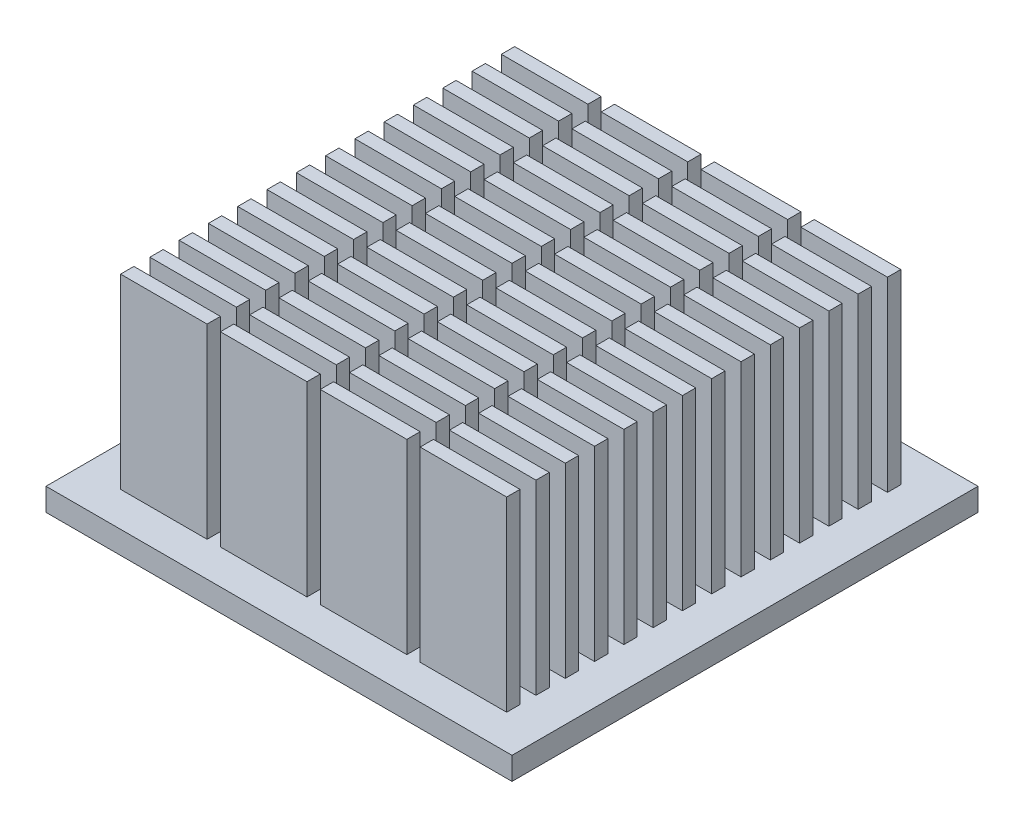
SolidWorks part; units mm, degrees
ref_plane "Front Plane" through (0, 0, 0) normal (0, 0, 1) x (1, 0, 0)
ref_plane "Top Plane" through (0, 0, 0) normal (0, 1, 0) x (1, 0, 0)
ref_plane "Right Plane" through (0, 0, 0) normal (1, 0, 0) x (0, 0, -1)
sketch "Sketch1" plane through (0, 0, 0) normal (0, 1, 0) x (1, 0, 0)
  line L1 (-17.5, -17.5) -> (17.5, -17.5)
  line L2 (-17.5, -17.5) -> (-17.5, 17.5)
  line L3 (-17.5, 17.5) -> (17.5, 17.5)
  line L4 (17.5, -17.5) -> (17.5, 17.5)
  line L5 (-17.5, -17.5) -> (17.5, 17.5) construction
  line L6 (-17.5, 17.5) -> (17.5, -17.5) construction
  point P0 (0, 0)
  dimension "D1" = 35
  dimension "D2" = 35
extrude "Boss-Extrude1" add sketch "Sketch1" along normal blind 1.7
sketch "Sketch2" plane through (0, 1.7, 0) normal (0, 1, 0) x (1, 0, 0)
  line L0 (-14.5, -0.7) -> (-8, -0.7)
  line L1 (-14.5, 1.5) -> (-8, 1.5)
  line L2 (-14.5, 1.5) -> (-14.5, 0.5)
  line L3 (-14.5, 0.5) -> (-8, 0.5)
  line L4 (-8, 1.5) -> (-8, 0.5)
  line L5 (-7, 1.5) -> (-0.5, 1.5)
  line L6 (-7, 1.5) -> (-7, 0.5)
  line L7 (-7, 0.5) -> (-0.5, 0.5)
  line L8 (-0.5, 1.5) -> (-0.5, 0.5)
  line L9 (0.5, 1.5) -> (7, 1.5)
  line L10 (0.5, 1.5) -> (0.5, 0.5)
  line L11 (0.5, 0.5) -> (7, 0.5)
  line L12 (7, 1.5) -> (7, 0.5)
  line L13 (8, 1.5) -> (14.5, 1.5)
  line L14 (8, 1.5) -> (8, 0.5)
  line L15 (8, 0.5) -> (14.5, 0.5)
  line L16 (14.5, 1.5) -> (14.5, 0.5)
  line L17 (-14.5, -0.7) -> (-14.5, -1.7)
  line L18 (-14.5, -1.7) -> (-8, -1.7)
  line L19 (-8, -0.7) -> (-8, -1.7)
  line L20 (-7, -0.7) -> (-0.5, -0.7)
  line L21 (-7, -0.7) -> (-7, -1.7)
  line L22 (-7, -1.7) -> (-0.5, -1.7)
  line L23 (-0.5, -0.7) -> (-0.5, -1.7)
  line L24 (0.5, -0.7) -> (7, -0.7)
  line L25 (0.5, -0.7) -> (0.5, -1.7)
  line L26 (0.5, -1.7) -> (7, -1.7)
  line L27 (7, -0.7) -> (7, -1.7)
  line L28 (8, -0.7) -> (14.5, -0.7)
  line L29 (8, -0.7) -> (8, -1.7)
  line L30 (8, -1.7) -> (14.5, -1.7)
  line L31 (14.5, -0.7) -> (14.5, -1.7)
  line L32 (-14.5, -2.9) -> (-8, -2.9)
  line L33 (-14.5, -2.9) -> (-14.5, -3.9)
  line L34 (-14.5, -3.9) -> (-8, -3.9)
  line L35 (-8, -2.9) -> (-8, -3.9)
  line L36 (-7, -2.9) -> (-0.5, -2.9)
  line L37 (-7, -2.9) -> (-7, -3.9)
  line L38 (-7, -3.9) -> (-0.5, -3.9)
  line L39 (-0.5, -2.9) -> (-0.5, -3.9)
  line L40 (0.5, -2.9) -> (7, -2.9)
  line L41 (0.5, -2.9) -> (0.5, -3.9)
  line L42 (0.5, -3.9) -> (7, -3.9)
  line L43 (7, -2.9) -> (7, -3.9)
  line L44 (8, -2.9) -> (14.5, -2.9)
  line L45 (8, -2.9) -> (8, -3.9)
  line L46 (8, -3.9) -> (14.5, -3.9)
  line L47 (14.5, -2.9) -> (14.5, -3.9)
  line L48 (-14.5, -5.1) -> (-8, -5.1)
  line L49 (-14.5, -5.1) -> (-14.5, -6.1)
  line L50 (-14.5, -6.1) -> (-8, -6.1)
  line L51 (-8, -5.1) -> (-8, -6.1)
  line L52 (-7, -5.1) -> (-0.5, -5.1)
  line L53 (-7, -5.1) -> (-7, -6.1)
  line L54 (-7, -6.1) -> (-0.5, -6.1)
  line L55 (-0.5, -5.1) -> (-0.5, -6.1)
  line L56 (0.5, -5.1) -> (7, -5.1)
  line L57 (0.5, -5.1) -> (0.5, -6.1)
  line L58 (0.5, -6.1) -> (7, -6.1)
  line L59 (7, -5.1) -> (7, -6.1)
  line L60 (8, -5.1) -> (14.5, -5.1)
  line L61 (8, -5.1) -> (8, -6.1)
  line L62 (8, -6.1) -> (14.5, -6.1)
  line L63 (14.5, -5.1) -> (14.5, -6.1)
  line L64 (-14.5, -7.3) -> (-8, -7.3)
  line L65 (-14.5, -7.3) -> (-14.5, -8.3)
  line L66 (-14.5, -8.3) -> (-8, -8.3)
  line L67 (-8, -7.3) -> (-8, -8.3)
  line L68 (-7, -7.3) -> (-0.5, -7.3)
  line L69 (-7, -7.3) -> (-7, -8.3)
  line L70 (-7, -8.3) -> (-0.5, -8.3)
  line L71 (-0.5, -7.3) -> (-0.5, -8.3)
  line L72 (0.5, -7.3) -> (7, -7.3)
  line L73 (0.5, -7.3) -> (0.5, -8.3)
  line L74 (0.5, -8.3) -> (7, -8.3)
  line L75 (7, -7.3) -> (7, -8.3)
  line L76 (8, -7.3) -> (14.5, -7.3)
  line L77 (8, -7.3) -> (8, -8.3)
  line L78 (8, -8.3) -> (14.5, -8.3)
  line L79 (14.5, -7.3) -> (14.5, -8.3)
  line L80 (-14.5, -9.5) -> (-8, -9.5)
  line L81 (-14.5, -9.5) -> (-14.5, -10.5)
  line L82 (-14.5, -10.5) -> (-8, -10.5)
  line L83 (-8, -9.5) -> (-8, -10.5)
  line L84 (-7, -9.5) -> (-0.5, -9.5)
  line L85 (-7, -9.5) -> (-7, -10.5)
  line L86 (-7, -10.5) -> (-0.5, -10.5)
  line L87 (-0.5, -9.5) -> (-0.5, -10.5)
  line L88 (0.5, -9.5) -> (7, -9.5)
  line L89 (0.5, -9.5) -> (0.5, -10.5)
  line L90 (0.5, -10.5) -> (7, -10.5)
  line L91 (7, -9.5) -> (7, -10.5)
  line L92 (8, -9.5) -> (14.5, -9.5)
  line L93 (8, -9.5) -> (8, -10.5)
  line L94 (8, -10.5) -> (14.5, -10.5)
  line L95 (14.5, -9.5) -> (14.5, -10.5)
  line L96 (-14.5, -11.7) -> (-8, -11.7)
  line L97 (-14.5, -11.7) -> (-14.5, -12.7)
  line L98 (-14.5, -12.7) -> (-8, -12.7)
  line L99 (-8, -11.7) -> (-8, -12.7)
  line L100 (-7, -11.7) -> (-0.5, -11.7)
  line L101 (-7, -11.7) -> (-7, -12.7)
  line L102 (-7, -12.7) -> (-0.5, -12.7)
  line L103 (-0.5, -11.7) -> (-0.5, -12.7)
  line L104 (0.5, -11.7) -> (7, -11.7)
  line L105 (0.5, -11.7) -> (0.5, -12.7)
  line L106 (0.5, -12.7) -> (7, -12.7)
  line L107 (7, -11.7) -> (7, -12.7)
  line L108 (8, -11.7) -> (14.5, -11.7)
  line L109 (8, -11.7) -> (8, -12.7)
  line L110 (8, -12.7) -> (14.5, -12.7)
  line L111 (14.5, -11.7) -> (14.5, -12.7)
  line L112 (-14.5, -13.9) -> (-8, -13.9)
  line L113 (-14.5, -13.9) -> (-14.5, -14.9)
  line L114 (-14.5, -14.9) -> (-8, -14.9)
  line L115 (-8, -13.9) -> (-8, -14.9)
  line L116 (-7, -13.9) -> (-0.5, -13.9)
  line L117 (-7, -13.9) -> (-7, -14.9)
  line L118 (-7, -14.9) -> (-0.5, -14.9)
  line L119 (-0.5, -13.9) -> (-0.5, -14.9)
  line L120 (0.5, -13.9) -> (7, -13.9)
  line L121 (0.5, -13.9) -> (0.5, -14.9)
  line L122 (0.5, -14.9) -> (7, -14.9)
  line L123 (7, -13.9) -> (7, -14.9)
  line L124 (8, -13.9) -> (14.5, -13.9)
  line L125 (8, -13.9) -> (8, -14.9)
  line L126 (8, -14.9) -> (14.5, -14.9)
  line L127 (14.5, -13.9) -> (14.5, -14.9)
  line L128 (-14.5, 1.5) -> (-8, 1.5)
  line L129 (-14.5, 1.5) -> (-14.5, 0.5)
  line L130 (-14.5, 0.5) -> (-8, 0.5)
  line L131 (-8, 1.5) -> (-8, 0.5)
  line L132 (-7, 1.5) -> (-0.5, 1.5)
  line L133 (-7, 1.5) -> (-7, 0.5)
  line L134 (-7, 0.5) -> (-0.5, 0.5)
  line L135 (-0.5, 1.5) -> (-0.5, 0.5)
  line L136 (0.5, 1.5) -> (7, 1.5)
  line L137 (0.5, 1.5) -> (0.5, 0.5)
  line L138 (0.5, 0.5) -> (7, 0.5)
  line L139 (7, 1.5) -> (7, 0.5)
  line L140 (8, 1.5) -> (14.5, 1.5)
  line L141 (8, 1.5) -> (8, 0.5)
  line L142 (8, 0.5) -> (14.5, 0.5)
  line L143 (14.5, 1.5) -> (14.5, 0.5)
  line L144 (-14.5, -0.7) -> (-8, -0.7)
  line L145 (-14.5, -0.7) -> (-14.5, -1.7)
  line L146 (-14.5, -1.7) -> (-8, -1.7)
  line L147 (-8, -0.7) -> (-8, -1.7)
  line L148 (-7, -0.7) -> (-0.5, -0.7)
  line L149 (-7, -0.7) -> (-7, -1.7)
  line L150 (-7, -1.7) -> (-0.5, -1.7)
  line L151 (-0.5, -0.7) -> (-0.5, -1.7)
  line L152 (0.5, -0.7) -> (7, -0.7)
  line L153 (0.5, -0.7) -> (0.5, -1.7)
  line L154 (0.5, -1.7) -> (7, -1.7)
  line L155 (7, -0.7) -> (7, -1.7)
  line L156 (8, -0.7) -> (14.5, -0.7)
  line L157 (8, -0.7) -> (8, -1.7)
  line L158 (8, -1.7) -> (14.5, -1.7)
  line L159 (14.5, -0.7) -> (14.5, -1.7)
  line L160 (-14.5, -2.9) -> (-8, -2.9)
  line L161 (-14.5, -2.9) -> (-14.5, -3.9)
  line L162 (-14.5, -3.9) -> (-8, -3.9)
  line L163 (-8, -2.9) -> (-8, -3.9)
  line L164 (-7, -2.9) -> (-0.5, -2.9)
  line L165 (-7, -2.9) -> (-7, -3.9)
  line L166 (-7, -3.9) -> (-0.5, -3.9)
  line L167 (-0.5, -2.9) -> (-0.5, -3.9)
  line L168 (0.5, -2.9) -> (7, -2.9)
  line L169 (0.5, -2.9) -> (0.5, -3.9)
  line L170 (0.5, -3.9) -> (7, -3.9)
  line L171 (7, -2.9) -> (7, -3.9)
  line L172 (8, -2.9) -> (14.5, -2.9)
  line L173 (8, -2.9) -> (8, -3.9)
  line L174 (8, -3.9) -> (14.5, -3.9)
  line L175 (14.5, -2.9) -> (14.5, -3.9)
  line L176 (-14.5, -5.1) -> (-8, -5.1)
  line L177 (-14.5, -5.1) -> (-14.5, -6.1)
  line L178 (-14.5, -6.1) -> (-8, -6.1)
  line L179 (-8, -5.1) -> (-8, -6.1)
  line L180 (-7, -5.1) -> (-0.5, -5.1)
  line L181 (-7, -5.1) -> (-7, -6.1)
  line L182 (-7, -6.1) -> (-0.5, -6.1)
  line L183 (-0.5, -5.1) -> (-0.5, -6.1)
  line L184 (0.5, -5.1) -> (7, -5.1)
  line L185 (0.5, -5.1) -> (0.5, -6.1)
  line L186 (0.5, -6.1) -> (7, -6.1)
  line L187 (7, -5.1) -> (7, -6.1)
  line L188 (8, -5.1) -> (14.5, -5.1)
  line L189 (8, -5.1) -> (8, -6.1)
  line L190 (8, -6.1) -> (14.5, -6.1)
  line L191 (14.5, -5.1) -> (14.5, -6.1)
  line L192 (-14.5, -7.3) -> (-8, -7.3)
  line L193 (-14.5, -7.3) -> (-14.5, -8.3)
  line L194 (-14.5, -8.3) -> (-8, -8.3)
  line L195 (-8, -7.3) -> (-8, -8.3)
  line L196 (-7, -7.3) -> (-0.5, -7.3)
  line L197 (-7, -7.3) -> (-7, -8.3)
  line L198 (-7, -8.3) -> (-0.5, -8.3)
  line L199 (-0.5, -7.3) -> (-0.5, -8.3)
  line L200 (0.5, -7.3) -> (7, -7.3)
  line L201 (0.5, -7.3) -> (0.5, -8.3)
  line L202 (0.5, -8.3) -> (7, -8.3)
  line L203 (7, -7.3) -> (7, -8.3)
  line L204 (8, -7.3) -> (14.5, -7.3)
  line L205 (8, -7.3) -> (8, -8.3)
  line L206 (8, -8.3) -> (14.5, -8.3)
  line L207 (14.5, -7.3) -> (14.5, -8.3)
  line L208 (-14.5, -9.5) -> (-8, -9.5)
  line L209 (-14.5, -9.5) -> (-14.5, -10.5)
  line L210 (-14.5, -10.5) -> (-8, -10.5)
  line L211 (-8, -9.5) -> (-8, -10.5)
  line L212 (-7, -9.5) -> (-0.5, -9.5)
  line L213 (-7, -9.5) -> (-7, -10.5)
  line L214 (-7, -10.5) -> (-0.5, -10.5)
  line L215 (-0.5, -9.5) -> (-0.5, -10.5)
  line L216 (0.5, -9.5) -> (7, -9.5)
  line L217 (0.5, -9.5) -> (0.5, -10.5)
  line L218 (0.5, -10.5) -> (7, -10.5)
  line L219 (7, -9.5) -> (7, -10.5)
  line L220 (8, -9.5) -> (14.5, -9.5)
  line L221 (8, -9.5) -> (8, -10.5)
  line L222 (8, -10.5) -> (14.5, -10.5)
  line L223 (14.5, -9.5) -> (14.5, -10.5)
  line L224 (-14.5, -11.7) -> (-8, -11.7)
  line L225 (-14.5, -11.7) -> (-14.5, -12.7)
  line L226 (-14.5, -12.7) -> (-8, -12.7)
  line L227 (-8, -11.7) -> (-8, -12.7)
  line L228 (-7, -11.7) -> (-0.5, -11.7)
  line L229 (-7, -11.7) -> (-7, -12.7)
  line L230 (-7, -12.7) -> (-0.5, -12.7)
  line L231 (-0.5, -11.7) -> (-0.5, -12.7)
  line L232 (0.5, -11.7) -> (7, -11.7)
  line L233 (0.5, -11.7) -> (0.5, -12.7)
  line L234 (0.5, -12.7) -> (7, -12.7)
  line L235 (7, -11.7) -> (7, -12.7)
  line L236 (8, -11.7) -> (14.5, -11.7)
  line L237 (8, -11.7) -> (8, -12.7)
  line L238 (8, -12.7) -> (14.5, -12.7)
  line L239 (14.5, -11.7) -> (14.5, -12.7)
  line L240 (-14.5, 3.7) -> (-8, 3.7)
  line L241 (-14.5, 3.7) -> (-14.5, 2.7)
  line L242 (-14.5, 2.7) -> (-8, 2.7)
  line L243 (-8, 3.7) -> (-8, 2.7)
  line L244 (-7, 3.7) -> (-0.5, 3.7)
  line L245 (-7, 3.7) -> (-7, 2.7)
  line L246 (-7, 2.7) -> (-0.5, 2.7)
  line L247 (-0.5, 3.7) -> (-0.5, 2.7)
  line L248 (0.5, 3.7) -> (7, 3.7)
  line L249 (0.5, 3.7) -> (0.5, 2.7)
  line L250 (0.5, 2.7) -> (7, 2.7)
  line L251 (7, 3.7) -> (7, 2.7)
  line L252 (8, 3.7) -> (14.5, 3.7)
  line L253 (8, 3.7) -> (8, 2.7)
  line L254 (8, 2.7) -> (14.5, 2.7)
  line L255 (14.5, 3.7) -> (14.5, 2.7)
  line L256 (-14.5, 1.5) -> (-8, 1.5)
  line L257 (-14.5, 1.5) -> (-14.5, 0.5)
  line L258 (-14.5, 0.5) -> (-8, 0.5)
  line L259 (-8, 1.5) -> (-8, 0.5)
  line L260 (-7, 1.5) -> (-0.5, 1.5)
  line L261 (-7, 1.5) -> (-7, 0.5)
  line L262 (-7, 0.5) -> (-0.5, 0.5)
  line L263 (-0.5, 1.5) -> (-0.5, 0.5)
  line L264 (0.5, 1.5) -> (7, 1.5)
  line L265 (0.5, 1.5) -> (0.5, 0.5)
  line L266 (0.5, 0.5) -> (7, 0.5)
  line L267 (7, 1.5) -> (7, 0.5)
  line L268 (8, 1.5) -> (14.5, 1.5)
  line L269 (8, 1.5) -> (8, 0.5)
  line L270 (8, 0.5) -> (14.5, 0.5)
  line L271 (14.5, 1.5) -> (14.5, 0.5)
  line L272 (-14.5, -0.7) -> (-8, -0.7)
  line L273 (-14.5, -0.7) -> (-14.5, -1.7)
  line L274 (-14.5, -1.7) -> (-8, -1.7)
  line L275 (-8, -0.7) -> (-8, -1.7)
  line L276 (-7, -0.7) -> (-0.5, -0.7)
  line L277 (-7, -0.7) -> (-7, -1.7)
  line L278 (-7, -1.7) -> (-0.5, -1.7)
  line L279 (-0.5, -0.7) -> (-0.5, -1.7)
  line L280 (0.5, -0.7) -> (7, -0.7)
  line L281 (0.5, -0.7) -> (0.5, -1.7)
  line L282 (0.5, -1.7) -> (7, -1.7)
  line L283 (7, -0.7) -> (7, -1.7)
  line L284 (8, -0.7) -> (14.5, -0.7)
  line L285 (8, -0.7) -> (8, -1.7)
  line L286 (8, -1.7) -> (14.5, -1.7)
  line L287 (14.5, -0.7) -> (14.5, -1.7)
  line L288 (-14.5, -2.9) -> (-8, -2.9)
  line L289 (-14.5, -2.9) -> (-14.5, -3.9)
  line L290 (-14.5, -3.9) -> (-8, -3.9)
  line L291 (-8, -2.9) -> (-8, -3.9)
  line L292 (-7, -2.9) -> (-0.5, -2.9)
  line L293 (-7, -2.9) -> (-7, -3.9)
  line L294 (-7, -3.9) -> (-0.5, -3.9)
  line L295 (-0.5, -2.9) -> (-0.5, -3.9)
  line L296 (0.5, -2.9) -> (7, -2.9)
  line L297 (0.5, -2.9) -> (0.5, -3.9)
  line L298 (0.5, -3.9) -> (7, -3.9)
  line L299 (7, -2.9) -> (7, -3.9)
  line L300 (8, -2.9) -> (14.5, -2.9)
  line L301 (8, -2.9) -> (8, -3.9)
  line L302 (8, -3.9) -> (14.5, -3.9)
  line L303 (14.5, -2.9) -> (14.5, -3.9)
  line L304 (-14.5, -5.1) -> (-8, -5.1)
  line L305 (-14.5, -5.1) -> (-14.5, -6.1)
  line L306 (-14.5, -6.1) -> (-8, -6.1)
  line L307 (-8, -5.1) -> (-8, -6.1)
  line L308 (-7, -5.1) -> (-0.5, -5.1)
  line L309 (-7, -5.1) -> (-7, -6.1)
  line L310 (-7, -6.1) -> (-0.5, -6.1)
  line L311 (-0.5, -5.1) -> (-0.5, -6.1)
  line L312 (0.5, -5.1) -> (7, -5.1)
  line L313 (0.5, -5.1) -> (0.5, -6.1)
  line L314 (0.5, -6.1) -> (7, -6.1)
  line L315 (7, -5.1) -> (7, -6.1)
  line L316 (8, -5.1) -> (14.5, -5.1)
  line L317 (8, -5.1) -> (8, -6.1)
  line L318 (8, -6.1) -> (14.5, -6.1)
  line L319 (14.5, -5.1) -> (14.5, -6.1)
  line L320 (-14.5, -7.3) -> (-8, -7.3)
  line L321 (-14.5, -7.3) -> (-14.5, -8.3)
  line L322 (-14.5, -8.3) -> (-8, -8.3)
  line L323 (-8, -7.3) -> (-8, -8.3)
  line L324 (-7, -7.3) -> (-0.5, -7.3)
  line L325 (-7, -7.3) -> (-7, -8.3)
  line L326 (-7, -8.3) -> (-0.5, -8.3)
  line L327 (-0.5, -7.3) -> (-0.5, -8.3)
  line L328 (0.5, -7.3) -> (7, -7.3)
  line L329 (0.5, -7.3) -> (0.5, -8.3)
  line L330 (0.5, -8.3) -> (7, -8.3)
  line L331 (7, -7.3) -> (7, -8.3)
  line L332 (8, -7.3) -> (14.5, -7.3)
  line L333 (8, -7.3) -> (8, -8.3)
  line L334 (8, -8.3) -> (14.5, -8.3)
  line L335 (14.5, -7.3) -> (14.5, -8.3)
  line L336 (-14.5, -9.5) -> (-8, -9.5)
  line L337 (-14.5, -9.5) -> (-14.5, -10.5)
  line L338 (-14.5, -10.5) -> (-8, -10.5)
  line L339 (-8, -9.5) -> (-8, -10.5)
  line L340 (-7, -9.5) -> (-0.5, -9.5)
  line L341 (-7, -9.5) -> (-7, -10.5)
  line L342 (-7, -10.5) -> (-0.5, -10.5)
  line L343 (-0.5, -9.5) -> (-0.5, -10.5)
  line L344 (0.5, -9.5) -> (7, -9.5)
  line L345 (0.5, -9.5) -> (0.5, -10.5)
  line L346 (0.5, -10.5) -> (7, -10.5)
  line L347 (7, -9.5) -> (7, -10.5)
  line L348 (8, -9.5) -> (14.5, -9.5)
  line L349 (8, -9.5) -> (8, -10.5)
  line L350 (8, -10.5) -> (14.5, -10.5)
  line L351 (14.5, -9.5) -> (14.5, -10.5)
  line L352 (-14.5, 5.9) -> (-8, 5.9)
  line L353 (-14.5, 5.9) -> (-14.5, 4.9)
  line L354 (-14.5, 4.9) -> (-8, 4.9)
  line L355 (-8, 5.9) -> (-8, 4.9)
  line L356 (-7, 5.9) -> (-0.5, 5.9)
  line L357 (-7, 5.9) -> (-7, 4.9)
  line L358 (-7, 4.9) -> (-0.5, 4.9)
  line L359 (-0.5, 5.9) -> (-0.5, 4.9)
  line L360 (0.5, 5.9) -> (7, 5.9)
  line L361 (0.5, 5.9) -> (0.5, 4.9)
  line L362 (0.5, 4.9) -> (7, 4.9)
  line L363 (7, 5.9) -> (7, 4.9)
  line L364 (8, 5.9) -> (14.5, 5.9)
  line L365 (8, 5.9) -> (8, 4.9)
  line L366 (8, 4.9) -> (14.5, 4.9)
  line L367 (14.5, 5.9) -> (14.5, 4.9)
  line L368 (-14.5, 3.7) -> (-8, 3.7)
  line L369 (-14.5, 3.7) -> (-14.5, 2.7)
  line L370 (-14.5, 2.7) -> (-8, 2.7)
  line L371 (-8, 3.7) -> (-8, 2.7)
  line L372 (-7, 3.7) -> (-0.5, 3.7)
  line L373 (-7, 3.7) -> (-7, 2.7)
  line L374 (-7, 2.7) -> (-0.5, 2.7)
  line L375 (-0.5, 3.7) -> (-0.5, 2.7)
  line L376 (0.5, 3.7) -> (7, 3.7)
  line L377 (0.5, 3.7) -> (0.5, 2.7)
  line L378 (0.5, 2.7) -> (7, 2.7)
  line L379 (7, 3.7) -> (7, 2.7)
  line L380 (8, 3.7) -> (14.5, 3.7)
  line L381 (8, 3.7) -> (8, 2.7)
  line L382 (8, 2.7) -> (14.5, 2.7)
  line L383 (14.5, 3.7) -> (14.5, 2.7)
  line L384 (-14.5, 1.5) -> (-8, 1.5)
  line L385 (-14.5, 1.5) -> (-14.5, 0.5)
  line L386 (-14.5, 0.5) -> (-8, 0.5)
  line L387 (-8, 1.5) -> (-8, 0.5)
  line L388 (-7, 1.5) -> (-0.5, 1.5)
  line L389 (-7, 1.5) -> (-7, 0.5)
  line L390 (-7, 0.5) -> (-0.5, 0.5)
  line L391 (-0.5, 1.5) -> (-0.5, 0.5)
  line L392 (0.5, 1.5) -> (7, 1.5)
  line L393 (0.5, 1.5) -> (0.5, 0.5)
  line L394 (0.5, 0.5) -> (7, 0.5)
  line L395 (7, 1.5) -> (7, 0.5)
  line L396 (8, 1.5) -> (14.5, 1.5)
  line L397 (8, 1.5) -> (8, 0.5)
  line L398 (8, 0.5) -> (14.5, 0.5)
  line L399 (14.5, 1.5) -> (14.5, 0.5)
  line L400 (-14.5, -0.7) -> (-8, -0.7)
  line L401 (-14.5, -0.7) -> (-14.5, -1.7)
  line L402 (-14.5, -1.7) -> (-8, -1.7)
  line L403 (-8, -0.7) -> (-8, -1.7)
  line L404 (-7, -0.7) -> (-0.5, -0.7)
  line L405 (-7, -0.7) -> (-7, -1.7)
  line L406 (-7, -1.7) -> (-0.5, -1.7)
  line L407 (-0.5, -0.7) -> (-0.5, -1.7)
  line L408 (0.5, -0.7) -> (7, -0.7)
  line L409 (0.5, -0.7) -> (0.5, -1.7)
  line L410 (0.5, -1.7) -> (7, -1.7)
  line L411 (7, -0.7) -> (7, -1.7)
  line L412 (8, -0.7) -> (14.5, -0.7)
  line L413 (8, -0.7) -> (8, -1.7)
  line L414 (8, -1.7) -> (14.5, -1.7)
  line L415 (14.5, -0.7) -> (14.5, -1.7)
  line L416 (-14.5, -2.9) -> (-8, -2.9)
  line L417 (-14.5, -2.9) -> (-14.5, -3.9)
  line L418 (-14.5, -3.9) -> (-8, -3.9)
  line L419 (-8, -2.9) -> (-8, -3.9)
  line L420 (-7, -2.9) -> (-0.5, -2.9)
  line L421 (-7, -2.9) -> (-7, -3.9)
  line L422 (-7, -3.9) -> (-0.5, -3.9)
  line L423 (-0.5, -2.9) -> (-0.5, -3.9)
  line L424 (0.5, -2.9) -> (7, -2.9)
  line L425 (0.5, -2.9) -> (0.5, -3.9)
  line L426 (0.5, -3.9) -> (7, -3.9)
  line L427 (7, -2.9) -> (7, -3.9)
  line L428 (8, -2.9) -> (14.5, -2.9)
  line L429 (8, -2.9) -> (8, -3.9)
  line L430 (8, -3.9) -> (14.5, -3.9)
  line L431 (14.5, -2.9) -> (14.5, -3.9)
  line L432 (-14.5, -5.1) -> (-8, -5.1)
  line L433 (-14.5, -5.1) -> (-14.5, -6.1)
  line L434 (-14.5, -6.1) -> (-8, -6.1)
  line L435 (-8, -5.1) -> (-8, -6.1)
  line L436 (-7, -5.1) -> (-0.5, -5.1)
  line L437 (-7, -5.1) -> (-7, -6.1)
  line L438 (-7, -6.1) -> (-0.5, -6.1)
  line L439 (-0.5, -5.1) -> (-0.5, -6.1)
  line L440 (0.5, -5.1) -> (7, -5.1)
  line L441 (0.5, -5.1) -> (0.5, -6.1)
  line L442 (0.5, -6.1) -> (7, -6.1)
  line L443 (7, -5.1) -> (7, -6.1)
  line L444 (8, -5.1) -> (14.5, -5.1)
  line L445 (8, -5.1) -> (8, -6.1)
  line L446 (8, -6.1) -> (14.5, -6.1)
  line L447 (14.5, -5.1) -> (14.5, -6.1)
  line L448 (-14.5, -7.3) -> (-8, -7.3)
  line L449 (-14.5, -7.3) -> (-14.5, -8.3)
  line L450 (-14.5, -8.3) -> (-8, -8.3)
  line L451 (-8, -7.3) -> (-8, -8.3)
  line L452 (-7, -7.3) -> (-0.5, -7.3)
  line L453 (-7, -7.3) -> (-7, -8.3)
  line L454 (-7, -8.3) -> (-0.5, -8.3)
  line L455 (-0.5, -7.3) -> (-0.5, -8.3)
  line L456 (0.5, -7.3) -> (7, -7.3)
  line L457 (0.5, -7.3) -> (0.5, -8.3)
  line L458 (0.5, -8.3) -> (7, -8.3)
  line L459 (7, -7.3) -> (7, -8.3)
  line L460 (8, -7.3) -> (14.5, -7.3)
  line L461 (8, -7.3) -> (8, -8.3)
  line L462 (8, -8.3) -> (14.5, -8.3)
  line L463 (14.5, -7.3) -> (14.5, -8.3)
  line L464 (-14.5, 8.1) -> (-8, 8.1)
  line L465 (-14.5, 8.1) -> (-14.5, 7.1)
  line L466 (-14.5, 7.1) -> (-8, 7.1)
  line L467 (-8, 8.1) -> (-8, 7.1)
  line L468 (-7, 8.1) -> (-0.5, 8.1)
  line L469 (-7, 8.1) -> (-7, 7.1)
  line L470 (-7, 7.1) -> (-0.5, 7.1)
  line L471 (-0.5, 8.1) -> (-0.5, 7.1)
  line L472 (0.5, 8.1) -> (7, 8.1)
  line L473 (0.5, 8.1) -> (0.5, 7.1)
  line L474 (0.5, 7.1) -> (7, 7.1)
  line L475 (7, 8.1) -> (7, 7.1)
  line L476 (8, 8.1) -> (14.5, 8.1)
  line L477 (8, 8.1) -> (8, 7.1)
  line L478 (8, 7.1) -> (14.5, 7.1)
  line L479 (14.5, 8.1) -> (14.5, 7.1)
  line L480 (-14.5, 5.9) -> (-8, 5.9)
  line L481 (-14.5, 5.9) -> (-14.5, 4.9)
  line L482 (-14.5, 4.9) -> (-8, 4.9)
  line L483 (-8, 5.9) -> (-8, 4.9)
  line L484 (-7, 5.9) -> (-0.5, 5.9)
  line L485 (-7, 5.9) -> (-7, 4.9)
  line L486 (-7, 4.9) -> (-0.5, 4.9)
  line L487 (-0.5, 5.9) -> (-0.5, 4.9)
  line L488 (0.5, 5.9) -> (7, 5.9)
  line L489 (0.5, 5.9) -> (0.5, 4.9)
  line L490 (0.5, 4.9) -> (7, 4.9)
  line L491 (7, 5.9) -> (7, 4.9)
  line L492 (8, 5.9) -> (14.5, 5.9)
  line L493 (8, 5.9) -> (8, 4.9)
  line L494 (8, 4.9) -> (14.5, 4.9)
  line L495 (14.5, 5.9) -> (14.5, 4.9)
  line L496 (-14.5, 3.7) -> (-8, 3.7)
  line L497 (-14.5, 3.7) -> (-14.5, 2.7)
  line L498 (-14.5, 2.7) -> (-8, 2.7)
  line L499 (-8, 3.7) -> (-8, 2.7)
  line L500 (-7, 3.7) -> (-0.5, 3.7)
  line L501 (-7, 3.7) -> (-7, 2.7)
  line L502 (-7, 2.7) -> (-0.5, 2.7)
  line L503 (-0.5, 3.7) -> (-0.5, 2.7)
  line L504 (0.5, 3.7) -> (7, 3.7)
  line L505 (0.5, 3.7) -> (0.5, 2.7)
  line L506 (0.5, 2.7) -> (7, 2.7)
  line L507 (7, 3.7) -> (7, 2.7)
  line L508 (8, 3.7) -> (14.5, 3.7)
  line L509 (8, 3.7) -> (8, 2.7)
  line L510 (8, 2.7) -> (14.5, 2.7)
  line L511 (14.5, 3.7) -> (14.5, 2.7)
  line L512 (-14.5, 1.5) -> (-8, 1.5)
  line L513 (-14.5, 1.5) -> (-14.5, 0.5)
  line L514 (-14.5, 0.5) -> (-8, 0.5)
  line L515 (-8, 1.5) -> (-8, 0.5)
  line L516 (-7, 1.5) -> (-0.5, 1.5)
  line L517 (-7, 1.5) -> (-7, 0.5)
  line L518 (-7, 0.5) -> (-0.5, 0.5)
  line L519 (-0.5, 1.5) -> (-0.5, 0.5)
  line L520 (0.5, 1.5) -> (7, 1.5)
  line L521 (0.5, 1.5) -> (0.5, 0.5)
  line L522 (0.5, 0.5) -> (7, 0.5)
  line L523 (7, 1.5) -> (7, 0.5)
  line L524 (8, 1.5) -> (14.5, 1.5)
  line L525 (8, 1.5) -> (8, 0.5)
  line L526 (8, 0.5) -> (14.5, 0.5)
  line L527 (14.5, 1.5) -> (14.5, 0.5)
  line L528 (-14.5, -0.7) -> (-8, -0.7)
  line L529 (-14.5, -0.7) -> (-14.5, -1.7)
  line L530 (-14.5, -1.7) -> (-8, -1.7)
  line L531 (-8, -0.7) -> (-8, -1.7)
  line L532 (-7, -0.7) -> (-0.5, -0.7)
  line L533 (-7, -0.7) -> (-7, -1.7)
  line L534 (-7, -1.7) -> (-0.5, -1.7)
  line L535 (-0.5, -0.7) -> (-0.5, -1.7)
  line L536 (0.5, -0.7) -> (7, -0.7)
  line L537 (0.5, -0.7) -> (0.5, -1.7)
  line L538 (0.5, -1.7) -> (7, -1.7)
  line L539 (7, -0.7) -> (7, -1.7)
  line L540 (8, -0.7) -> (14.5, -0.7)
  line L541 (8, -0.7) -> (8, -1.7)
  line L542 (8, -1.7) -> (14.5, -1.7)
  line L543 (14.5, -0.7) -> (14.5, -1.7)
  line L544 (-14.5, -2.9) -> (-8, -2.9)
  line L545 (-14.5, -2.9) -> (-14.5, -3.9)
  line L546 (-14.5, -3.9) -> (-8, -3.9)
  line L547 (-8, -2.9) -> (-8, -3.9)
  line L548 (-7, -2.9) -> (-0.5, -2.9)
  line L549 (-7, -2.9) -> (-7, -3.9)
  line L550 (-7, -3.9) -> (-0.5, -3.9)
  line L551 (-0.5, -2.9) -> (-0.5, -3.9)
  line L552 (0.5, -2.9) -> (7, -2.9)
  line L553 (0.5, -2.9) -> (0.5, -3.9)
  line L554 (0.5, -3.9) -> (7, -3.9)
  line L555 (7, -2.9) -> (7, -3.9)
  line L556 (8, -2.9) -> (14.5, -2.9)
  line L557 (8, -2.9) -> (8, -3.9)
  line L558 (8, -3.9) -> (14.5, -3.9)
  line L559 (14.5, -2.9) -> (14.5, -3.9)
  line L560 (-14.5, -5.1) -> (-8, -5.1)
  line L561 (-14.5, -5.1) -> (-14.5, -6.1)
  line L562 (-14.5, -6.1) -> (-8, -6.1)
  line L563 (-8, -5.1) -> (-8, -6.1)
  line L564 (-7, -5.1) -> (-0.5, -5.1)
  line L565 (-7, -5.1) -> (-7, -6.1)
  line L566 (-7, -6.1) -> (-0.5, -6.1)
  line L567 (-0.5, -5.1) -> (-0.5, -6.1)
  line L568 (0.5, -5.1) -> (7, -5.1)
  line L569 (0.5, -5.1) -> (0.5, -6.1)
  line L570 (0.5, -6.1) -> (7, -6.1)
  line L571 (7, -5.1) -> (7, -6.1)
  line L572 (8, -5.1) -> (14.5, -5.1)
  line L573 (8, -5.1) -> (8, -6.1)
  line L574 (8, -6.1) -> (14.5, -6.1)
  line L575 (14.5, -5.1) -> (14.5, -6.1)
  line L576 (-14.5, 10.3) -> (-8, 10.3)
  line L577 (-14.5, 10.3) -> (-14.5, 9.3)
  line L578 (-14.5, 9.3) -> (-8, 9.3)
  line L579 (-8, 10.3) -> (-8, 9.3)
  line L580 (-7, 10.3) -> (-0.5, 10.3)
  line L581 (-7, 10.3) -> (-7, 9.3)
  line L582 (-7, 9.3) -> (-0.5, 9.3)
  line L583 (-0.5, 10.3) -> (-0.5, 9.3)
  line L584 (0.5, 10.3) -> (7, 10.3)
  line L585 (0.5, 10.3) -> (0.5, 9.3)
  line L586 (0.5, 9.3) -> (7, 9.3)
  line L587 (7, 10.3) -> (7, 9.3)
  line L588 (8, 10.3) -> (14.5, 10.3)
  line L589 (8, 10.3) -> (8, 9.3)
  line L590 (8, 9.3) -> (14.5, 9.3)
  line L591 (14.5, 10.3) -> (14.5, 9.3)
  line L592 (-14.5, 8.1) -> (-8, 8.1)
  line L593 (-14.5, 8.1) -> (-14.5, 7.1)
  line L594 (-14.5, 7.1) -> (-8, 7.1)
  line L595 (-8, 8.1) -> (-8, 7.1)
  line L596 (-7, 8.1) -> (-0.5, 8.1)
  line L597 (-7, 8.1) -> (-7, 7.1)
  line L598 (-7, 7.1) -> (-0.5, 7.1)
  line L599 (-0.5, 8.1) -> (-0.5, 7.1)
  line L600 (0.5, 8.1) -> (7, 8.1)
  line L601 (0.5, 8.1) -> (0.5, 7.1)
  line L602 (0.5, 7.1) -> (7, 7.1)
  line L603 (7, 8.1) -> (7, 7.1)
  line L604 (8, 8.1) -> (14.5, 8.1)
  line L605 (8, 8.1) -> (8, 7.1)
  line L606 (8, 7.1) -> (14.5, 7.1)
  line L607 (14.5, 8.1) -> (14.5, 7.1)
  line L608 (-14.5, 5.9) -> (-8, 5.9)
  line L609 (-14.5, 5.9) -> (-14.5, 4.9)
  line L610 (-14.5, 4.9) -> (-8, 4.9)
  line L611 (-8, 5.9) -> (-8, 4.9)
  line L612 (-7, 5.9) -> (-0.5, 5.9)
  line L613 (-7, 5.9) -> (-7, 4.9)
  line L614 (-7, 4.9) -> (-0.5, 4.9)
  line L615 (-0.5, 5.9) -> (-0.5, 4.9)
  line L616 (0.5, 5.9) -> (7, 5.9)
  line L617 (0.5, 5.9) -> (0.5, 4.9)
  line L618 (0.5, 4.9) -> (7, 4.9)
  line L619 (7, 5.9) -> (7, 4.9)
  line L620 (8, 5.9) -> (14.5, 5.9)
  line L621 (8, 5.9) -> (8, 4.9)
  line L622 (8, 4.9) -> (14.5, 4.9)
  line L623 (14.5, 5.9) -> (14.5, 4.9)
  line L624 (-14.5, 3.7) -> (-8, 3.7)
  line L625 (-14.5, 3.7) -> (-14.5, 2.7)
  line L626 (-14.5, 2.7) -> (-8, 2.7)
  line L627 (-8, 3.7) -> (-8, 2.7)
  line L628 (-7, 3.7) -> (-0.5, 3.7)
  line L629 (-7, 3.7) -> (-7, 2.7)
  line L630 (-7, 2.7) -> (-0.5, 2.7)
  line L631 (-0.5, 3.7) -> (-0.5, 2.7)
  line L632 (0.5, 3.7) -> (7, 3.7)
  line L633 (0.5, 3.7) -> (0.5, 2.7)
  line L634 (0.5, 2.7) -> (7, 2.7)
  line L635 (7, 3.7) -> (7, 2.7)
  line L636 (8, 3.7) -> (14.5, 3.7)
  line L637 (8, 3.7) -> (8, 2.7)
  line L638 (8, 2.7) -> (14.5, 2.7)
  line L639 (14.5, 3.7) -> (14.5, 2.7)
  line L640 (-14.5, 1.5) -> (-8, 1.5)
  line L641 (-14.5, 1.5) -> (-14.5, 0.5)
  line L642 (-14.5, 0.5) -> (-8, 0.5)
  line L643 (-8, 1.5) -> (-8, 0.5)
  line L644 (-7, 1.5) -> (-0.5, 1.5)
  line L645 (-7, 1.5) -> (-7, 0.5)
  line L646 (-7, 0.5) -> (-0.5, 0.5)
  line L647 (-0.5, 1.5) -> (-0.5, 0.5)
  line L648 (0.5, 1.5) -> (7, 1.5)
  line L649 (0.5, 1.5) -> (0.5, 0.5)
  line L650 (0.5, 0.5) -> (7, 0.5)
  line L651 (7, 1.5) -> (7, 0.5)
  line L652 (8, 1.5) -> (14.5, 1.5)
  line L653 (8, 1.5) -> (8, 0.5)
  line L654 (8, 0.5) -> (14.5, 0.5)
  line L655 (14.5, 1.5) -> (14.5, 0.5)
  line L656 (-14.5, -0.7) -> (-8, -0.7)
  line L657 (-14.5, -0.7) -> (-14.5, -1.7)
  line L658 (-14.5, -1.7) -> (-8, -1.7)
  line L659 (-8, -0.7) -> (-8, -1.7)
  line L660 (-7, -0.7) -> (-0.5, -0.7)
  line L661 (-7, -0.7) -> (-7, -1.7)
  line L662 (-7, -1.7) -> (-0.5, -1.7)
  line L663 (-0.5, -0.7) -> (-0.5, -1.7)
  line L664 (0.5, -0.7) -> (7, -0.7)
  line L665 (0.5, -0.7) -> (0.5, -1.7)
  line L666 (0.5, -1.7) -> (7, -1.7)
  line L667 (7, -0.7) -> (7, -1.7)
  line L668 (8, -0.7) -> (14.5, -0.7)
  line L669 (8, -0.7) -> (8, -1.7)
  line L670 (8, -1.7) -> (14.5, -1.7)
  line L671 (14.5, -0.7) -> (14.5, -1.7)
  line L672 (-14.5, -2.9) -> (-8, -2.9)
  line L673 (-14.5, -2.9) -> (-14.5, -3.9)
  line L674 (-14.5, -3.9) -> (-8, -3.9)
  line L675 (-8, -2.9) -> (-8, -3.9)
  line L676 (-7, -2.9) -> (-0.5, -2.9)
  line L677 (-7, -2.9) -> (-7, -3.9)
  line L678 (-7, -3.9) -> (-0.5, -3.9)
  line L679 (-0.5, -2.9) -> (-0.5, -3.9)
  line L680 (0.5, -2.9) -> (7, -2.9)
  line L681 (0.5, -2.9) -> (0.5, -3.9)
  line L682 (0.5, -3.9) -> (7, -3.9)
  line L683 (7, -2.9) -> (7, -3.9)
  line L684 (8, -2.9) -> (14.5, -2.9)
  line L685 (8, -2.9) -> (8, -3.9)
  line L686 (8, -3.9) -> (14.5, -3.9)
  line L687 (14.5, -2.9) -> (14.5, -3.9)
  line L688 (-14.5, 12.5) -> (-8, 12.5)
  line L689 (-14.5, 12.5) -> (-14.5, 11.5)
  line L690 (-14.5, 11.5) -> (-8, 11.5)
  line L691 (-8, 12.5) -> (-8, 11.5)
  line L692 (-7, 12.5) -> (-0.5, 12.5)
  line L693 (-7, 12.5) -> (-7, 11.5)
  line L694 (-7, 11.5) -> (-0.5, 11.5)
  line L695 (-0.5, 12.5) -> (-0.5, 11.5)
  line L696 (0.5, 12.5) -> (7, 12.5)
  line L697 (0.5, 12.5) -> (0.5, 11.5)
  line L698 (0.5, 11.5) -> (7, 11.5)
  line L699 (7, 12.5) -> (7, 11.5)
  line L700 (8, 12.5) -> (14.5, 12.5)
  line L701 (8, 12.5) -> (8, 11.5)
  line L702 (8, 11.5) -> (14.5, 11.5)
  line L703 (14.5, 12.5) -> (14.5, 11.5)
  line L704 (-14.5, 10.3) -> (-8, 10.3)
  line L705 (-14.5, 10.3) -> (-14.5, 9.3)
  line L706 (-14.5, 9.3) -> (-8, 9.3)
  line L707 (-8, 10.3) -> (-8, 9.3)
  line L708 (-7, 10.3) -> (-0.5, 10.3)
  line L709 (-7, 10.3) -> (-7, 9.3)
  line L710 (-7, 9.3) -> (-0.5, 9.3)
  line L711 (-0.5, 10.3) -> (-0.5, 9.3)
  line L712 (0.5, 10.3) -> (7, 10.3)
  line L713 (0.5, 10.3) -> (0.5, 9.3)
  line L714 (0.5, 9.3) -> (7, 9.3)
  line L715 (7, 10.3) -> (7, 9.3)
  line L716 (8, 10.3) -> (14.5, 10.3)
  line L717 (8, 10.3) -> (8, 9.3)
  line L718 (8, 9.3) -> (14.5, 9.3)
  line L719 (14.5, 10.3) -> (14.5, 9.3)
  line L720 (-14.5, 8.1) -> (-8, 8.1)
  line L721 (-14.5, 8.1) -> (-14.5, 7.1)
  line L722 (-14.5, 7.1) -> (-8, 7.1)
  line L723 (-8, 8.1) -> (-8, 7.1)
  line L724 (-7, 8.1) -> (-0.5, 8.1)
  line L725 (-7, 8.1) -> (-7, 7.1)
  line L726 (-7, 7.1) -> (-0.5, 7.1)
  line L727 (-0.5, 8.1) -> (-0.5, 7.1)
  line L728 (0.5, 8.1) -> (7, 8.1)
  line L729 (0.5, 8.1) -> (0.5, 7.1)
  line L730 (0.5, 7.1) -> (7, 7.1)
  line L731 (7, 8.1) -> (7, 7.1)
  line L732 (8, 8.1) -> (14.5, 8.1)
  line L733 (8, 8.1) -> (8, 7.1)
  line L734 (8, 7.1) -> (14.5, 7.1)
  line L735 (14.5, 8.1) -> (14.5, 7.1)
  line L736 (-14.5, 5.9) -> (-8, 5.9)
  line L737 (-14.5, 5.9) -> (-14.5, 4.9)
  line L738 (-14.5, 4.9) -> (-8, 4.9)
  line L739 (-8, 5.9) -> (-8, 4.9)
  line L740 (-7, 5.9) -> (-0.5, 5.9)
  line L741 (-7, 5.9) -> (-7, 4.9)
  line L742 (-7, 4.9) -> (-0.5, 4.9)
  line L743 (-0.5, 5.9) -> (-0.5, 4.9)
  line L744 (0.5, 5.9) -> (7, 5.9)
  line L745 (0.5, 5.9) -> (0.5, 4.9)
  line L746 (0.5, 4.9) -> (7, 4.9)
  line L747 (7, 5.9) -> (7, 4.9)
  line L748 (8, 5.9) -> (14.5, 5.9)
  line L749 (8, 5.9) -> (8, 4.9)
  line L750 (8, 4.9) -> (14.5, 4.9)
  line L751 (14.5, 5.9) -> (14.5, 4.9)
  line L752 (-14.5, 3.7) -> (-8, 3.7)
  line L753 (-14.5, 3.7) -> (-14.5, 2.7)
  line L754 (-14.5, 2.7) -> (-8, 2.7)
  line L755 (-8, 3.7) -> (-8, 2.7)
  line L756 (-7, 3.7) -> (-0.5, 3.7)
  line L757 (-7, 3.7) -> (-7, 2.7)
  line L758 (-7, 2.7) -> (-0.5, 2.7)
  line L759 (-0.5, 3.7) -> (-0.5, 2.7)
  line L760 (0.5, 3.7) -> (7, 3.7)
  line L761 (0.5, 3.7) -> (0.5, 2.7)
  line L762 (0.5, 2.7) -> (7, 2.7)
  line L763 (7, 3.7) -> (7, 2.7)
  line L764 (8, 3.7) -> (14.5, 3.7)
  line L765 (8, 3.7) -> (8, 2.7)
  line L766 (8, 2.7) -> (14.5, 2.7)
  line L767 (14.5, 3.7) -> (14.5, 2.7)
  line L768 (-14.5, 1.5) -> (-8, 1.5)
  line L769 (-14.5, 1.5) -> (-14.5, 0.5)
  line L770 (-14.5, 0.5) -> (-8, 0.5)
  line L771 (-8, 1.5) -> (-8, 0.5)
  line L772 (-7, 1.5) -> (-0.5, 1.5)
  line L773 (-7, 1.5) -> (-7, 0.5)
  line L774 (-7, 0.5) -> (-0.5, 0.5)
  line L775 (-0.5, 1.5) -> (-0.5, 0.5)
  line L776 (0.5, 1.5) -> (7, 1.5)
  line L777 (0.5, 1.5) -> (0.5, 0.5)
  line L778 (0.5, 0.5) -> (7, 0.5)
  line L779 (7, 1.5) -> (7, 0.5)
  line L780 (8, 1.5) -> (14.5, 1.5)
  line L781 (8, 1.5) -> (8, 0.5)
  line L782 (8, 0.5) -> (14.5, 0.5)
  line L783 (14.5, 1.5) -> (14.5, 0.5)
  line L784 (-14.5, -0.7) -> (-8, -0.7)
  line L785 (-14.5, -0.7) -> (-14.5, -1.7)
  line L786 (-14.5, -1.7) -> (-8, -1.7)
  line L787 (-8, -0.7) -> (-8, -1.7)
  line L788 (-7, -0.7) -> (-0.5, -0.7)
  line L789 (-7, -0.7) -> (-7, -1.7)
  line L790 (-7, -1.7) -> (-0.5, -1.7)
  line L791 (-0.5, -0.7) -> (-0.5, -1.7)
  line L792 (0.5, -0.7) -> (7, -0.7)
  line L793 (0.5, -0.7) -> (0.5, -1.7)
  line L794 (0.5, -1.7) -> (7, -1.7)
  line L795 (7, -0.7) -> (7, -1.7)
  line L796 (8, -0.7) -> (14.5, -0.7)
  line L797 (8, -0.7) -> (8, -1.7)
  line L798 (8, -1.7) -> (14.5, -1.7)
  line L799 (14.5, -0.7) -> (14.5, -1.7)
  line L800 (-14.5, 3.7) -> (-8, 3.7)
  line L801 (-14.5, 3.7) -> (-14.5, 2.7)
  line L802 (-14.5, 2.7) -> (-8, 2.7)
  line L803 (-8, 3.7) -> (-8, 2.7)
  line L804 (-7, 3.7) -> (-0.5, 3.7)
  line L805 (-7, 3.7) -> (-7, 2.7)
  line L806 (-7, 2.7) -> (-0.5, 2.7)
  line L807 (-0.5, 3.7) -> (-0.5, 2.7)
  line L808 (0.5, 3.7) -> (7, 3.7)
  line L809 (0.5, 3.7) -> (0.5, 2.7)
  line L810 (0.5, 2.7) -> (7, 2.7)
  line L811 (7, 3.7) -> (7, 2.7)
  line L812 (8, 3.7) -> (14.5, 3.7)
  line L813 (8, 3.7) -> (8, 2.7)
  line L814 (8, 2.7) -> (14.5, 2.7)
  line L815 (14.5, 3.7) -> (14.5, 2.7)
  line L816 (-14.5, 5.9) -> (-8, 5.9)
  line L817 (-14.5, 5.9) -> (-14.5, 4.9)
  line L818 (-14.5, 4.9) -> (-8, 4.9)
  line L819 (-8, 5.9) -> (-8, 4.9)
  line L820 (-7, 5.9) -> (-0.5, 5.9)
  line L821 (-7, 5.9) -> (-7, 4.9)
  line L822 (-7, 4.9) -> (-0.5, 4.9)
  line L823 (-0.5, 5.9) -> (-0.5, 4.9)
  line L824 (0.5, 5.9) -> (7, 5.9)
  line L825 (0.5, 5.9) -> (0.5, 4.9)
  line L826 (0.5, 4.9) -> (7, 4.9)
  line L827 (7, 5.9) -> (7, 4.9)
  line L828 (8, 5.9) -> (14.5, 5.9)
  line L829 (8, 5.9) -> (8, 4.9)
  line L830 (8, 4.9) -> (14.5, 4.9)
  line L831 (14.5, 5.9) -> (14.5, 4.9)
  line L832 (-14.5, 8.1) -> (-8, 8.1)
  line L833 (-14.5, 8.1) -> (-14.5, 7.1)
  line L834 (-14.5, 7.1) -> (-8, 7.1)
  line L835 (-8, 8.1) -> (-8, 7.1)
  line L836 (-7, 8.1) -> (-0.5, 8.1)
  line L837 (-7, 8.1) -> (-7, 7.1)
  line L838 (-7, 7.1) -> (-0.5, 7.1)
  line L839 (-0.5, 8.1) -> (-0.5, 7.1)
  line L840 (0.5, 8.1) -> (7, 8.1)
  line L841 (0.5, 8.1) -> (0.5, 7.1)
  line L842 (0.5, 7.1) -> (7, 7.1)
  line L843 (7, 8.1) -> (7, 7.1)
  line L844 (8, 8.1) -> (14.5, 8.1)
  line L845 (8, 8.1) -> (8, 7.1)
  line L846 (8, 7.1) -> (14.5, 7.1)
  line L847 (14.5, 8.1) -> (14.5, 7.1)
  line L848 (-14.5, 10.3) -> (-8, 10.3)
  line L849 (-14.5, 10.3) -> (-14.5, 9.3)
  line L850 (-14.5, 9.3) -> (-8, 9.3)
  line L851 (-8, 10.3) -> (-8, 9.3)
  line L852 (-7, 10.3) -> (-0.5, 10.3)
  line L853 (-7, 10.3) -> (-7, 9.3)
  line L854 (-7, 9.3) -> (-0.5, 9.3)
  line L855 (-0.5, 10.3) -> (-0.5, 9.3)
  line L856 (0.5, 10.3) -> (7, 10.3)
  line L857 (0.5, 10.3) -> (0.5, 9.3)
  line L858 (0.5, 9.3) -> (7, 9.3)
  line L859 (7, 10.3) -> (7, 9.3)
  line L860 (8, 10.3) -> (14.5, 10.3)
  line L861 (8, 10.3) -> (8, 9.3)
  line L862 (8, 9.3) -> (14.5, 9.3)
  line L863 (14.5, 10.3) -> (14.5, 9.3)
  line L864 (-14.5, 12.5) -> (-8, 12.5)
  line L865 (-14.5, 12.5) -> (-14.5, 11.5)
  line L866 (-14.5, 11.5) -> (-8, 11.5)
  line L867 (-8, 12.5) -> (-8, 11.5)
  line L868 (-7, 12.5) -> (-0.5, 12.5)
  line L869 (-7, 12.5) -> (-7, 11.5)
  line L870 (-7, 11.5) -> (-0.5, 11.5)
  line L871 (-0.5, 12.5) -> (-0.5, 11.5)
  line L872 (0.5, 12.5) -> (7, 12.5)
  line L873 (0.5, 12.5) -> (0.5, 11.5)
  line L874 (0.5, 11.5) -> (7, 11.5)
  line L875 (7, 12.5) -> (7, 11.5)
  line L876 (8, 12.5) -> (14.5, 12.5)
  line L877 (8, 12.5) -> (8, 11.5)
  line L878 (8, 11.5) -> (14.5, 11.5)
  line L879 (14.5, 12.5) -> (14.5, 11.5)
  line L880 (-14.5, 14.7) -> (-8, 14.7)
  line L881 (-14.5, 14.7) -> (-14.5, 13.7)
  line L882 (-14.5, 13.7) -> (-8, 13.7)
  line L883 (-8, 14.7) -> (-8, 13.7)
  line L884 (-7, 14.7) -> (-0.5, 14.7)
  line L885 (-7, 14.7) -> (-7, 13.7)
  line L886 (-7, 13.7) -> (-0.5, 13.7)
  line L887 (-0.5, 14.7) -> (-0.5, 13.7)
  line L888 (0.5, 14.7) -> (7, 14.7)
  line L889 (0.5, 14.7) -> (0.5, 13.7)
  line L890 (0.5, 13.7) -> (7, 13.7)
  line L891 (7, 14.7) -> (7, 13.7)
  line L892 (8, 14.7) -> (14.5, 14.7)
  line L893 (8, 14.7) -> (8, 13.7)
  line L894 (8, 13.7) -> (14.5, 13.7)
  line L895 (14.5, 14.7) -> (14.5, 13.7)
  dimension "D1" = 0.5
  dimension "D2" = 0.5
  dimension "D3" = 1
  dimension "D4" = 1
  dimension "D5" = 6.5
  dimension "D6" = 6.5
  dimension "D7" = 6.5
  dimension "D8" = 6.5
  dimension "D9" = 1
  dimension "D10" = 1
  dimension "D11" = 1
  dimension "D12" = 1
  dimension "D13" = 0.5
  dimension "D14" = 0.5
  dimension "D15" = 0.5
  dimension "D16" = 0.5
  dimension "D18" = 8
  dimension "D17" = 7
extrude "Boss-Extrude2" add sketch "Sketch2" along normal blind 14
